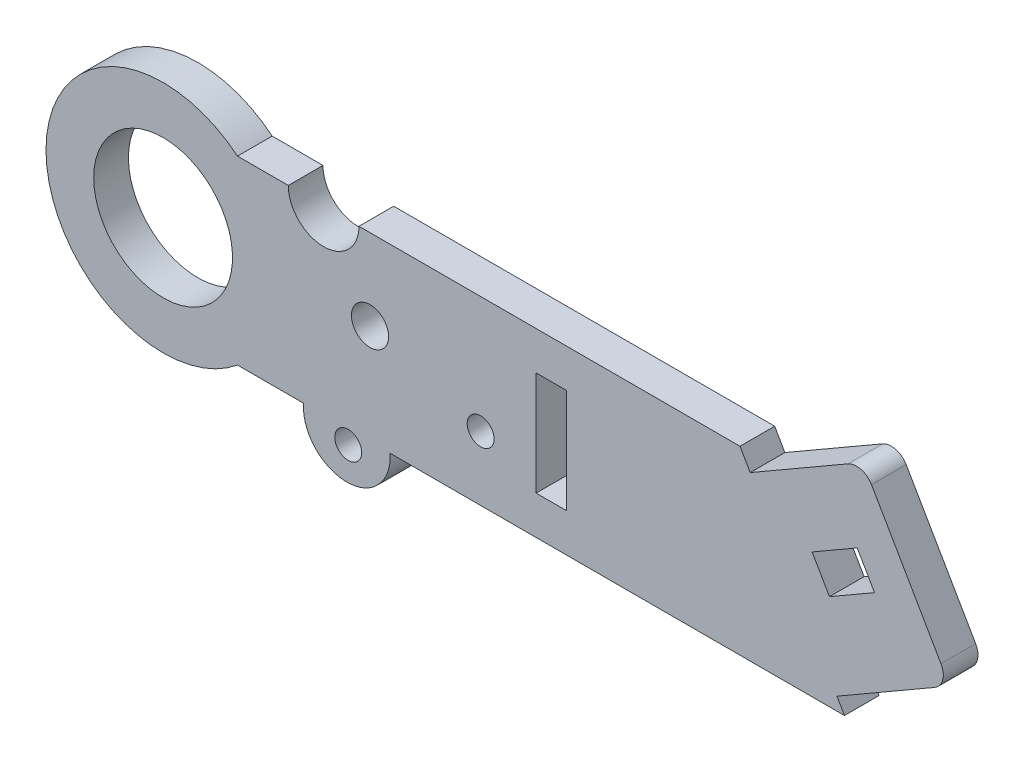
SolidWorks part; units mm, degrees
ref_plane "Ebene vorne" through (0, 0, 0) normal (0, 0, 1) x (1, 0, 0)
ref_plane "Ebene oben" through (0, 0, 0) normal (0, 1, 0) x (1, 0, 0)
ref_plane "Ebene rechts" through (0, 0, 0) normal (1, 0, 0) x (0, 0, -1)
sketch "Skizze1" plane through (0, 0, 0) normal (0, 0, 1) x (1, 0, 0)
  line L0 (8.5706, -10.4305) -> (-71.4294, -10.4305)
  line L7 (-71.4294, 10.4305) -> (-65.5753, 10.4305)
  line L8 (-57.4235, 10.4305) -> (8.5706, 10.4305)
  line L9 (-106.0055, 0) -> (28.1497, 0) construction
  arc A3 (-65.5753, 10.4305) -> (-57.4235, 10.4305) centre (-61.4994, 10.4305) ccw
  arc A6 (-71.4294, 10.4305) -> (-71.4294, -10.4305) centre (-80, 0) ccw
  arc A7 (8.5706, 10.4305) -> (8.5706, -10.4305) centre (8.5706, 0) cw
  dimension "D4" = 5.8542
  dimension "D2" = 20.861
  dimension "D1" = 13.5
  dimension "D3" = 4.0759
  dimension "D5" = 80
  dimension "D6" = 10.4305
extrude "Aufsatz-Linear austragen1" add sketch "Skizze1" along normal blind 4
sketch "Skizze2" plane through (0, 0, 4) normal (0, 0, 1) x (1, 0, 0)
  line L0 (-5.1962, 4.0336) -> (0, 7.0336)
  line L5 (-5.1962, 4.0336) -> (-3.1962, 0.5695)
  line L6 (0, 7.0336) -> (2, 3.5695)
  line L7 (-3.1962, 0.5695) -> (2, 3.5695)
  line L8 (-71.4294, -10.4305) -> (8.5706, -10.4305) construction
  line L9 (8.5706, 10.4305) -> (-57.4235, 10.4305) construction
  circle A1 centre (-80, 0) radius 8
  circle A2 centre (-56.1528, 1.1059) radius 2.1413
  dimension "D1" = 4
  dimension "D2" = 16
  dimension "D8" = 4.2826
  dimension "D3" = 6
  dimension "D4" = 14
  dimension "D5" = 80
  dimension "D6" = 56.1528
  dimension "D7" = 1.1059
  dimension "D9" = 2
  dimension "D10" = 60
extrude "Schnitt-Linear austragen1" cut sketch "Skizze2" against normal up to next
sketch "Skizze3" plane through (0, 0, 4) normal (0, 0, 1) x (1, 0, 0)
  line L0 (12.9867, 30.6283) -> (33.0198, -4.07)
  line L1 (-2.3301, -8.9305) -> (8.9282, -2.4305)
  line L2 (-15.6304, 14.1062) -> (-12.3301, 8.39)
  line L7 (-2.3301, -8.9305) -> (4.4027, -20.5921)
  line L8 (-15.6304, 14.1062) -> (12.9867, 30.6283)
  line L10 (33.0198, -4.07) -> (4.4027, -20.5921)
  line L11 (-5.1962, 4.0336) -> (-3.1962, 0.5695) construction
  line L12 (8.9282, -2.4305) -> (-1.0718, 14.89)
  line L13 (-1.0718, 14.89) -> (-12.3301, 8.39)
  line L14 (-71.4294, -10.4305) -> (8.5706, -10.4305) construction
  dimension "D1" = 20
  dimension "D2" = 1.5
  dimension "D3" = 4
  dimension "D4" = 13
extrude "Schnitt-Linear austragen2" cut sketch "Skizze3" against normal up to next
sketch "Skizze4" plane through (0, 0, 0) normal (0, 0, 1) x (1, 0, 0)
  line L0 (-8.7958, 10.4305) -> (-1.0718, 14.89)
  line L1 (1.6498, 14.1761) -> (9.6603, 0.3015)
  line L3 (-8.7958, 10.4305) -> (1.5029, 10.4305)
  line L4 (1.5029, 10.4305) -> (8.9282, -2.4305)
  line L5 (-2.3301, -8.9305) -> (-1.4641, -10.4305) construction
  arc A0 (8.9282, -2.4305) -> (9.6603, 0.3015) centre (7.9282, -0.6985) ccw
  arc A1 (-1.0718, 14.89) -> (1.6498, 14.1761) centre (-0.0717, 13.158) cw
  dimension "D2" = 2
  dimension "D3" = 2
  dimension "D1" = 15
extrude "Aufsatz-Linear austragen3" add sketch "Skizze4" along normal up to surface (4 mm away) up to face at (-54.0115, 1.1059, 4)
sketch "Skizze5" plane through (0, 0, 4) normal (0, 0, 1) x (1, 0, 0)
  line L0 (19.551, 0) -> (-121.594, 0) construction
  line L1 (-37.0082, 6) -> (-33.5082, 6)
  line L2 (-37.0082, 6) -> (-37.0082, -6)
  line L3 (-37.0082, -6) -> (-33.5082, -6)
  line L4 (-33.5082, 6) -> (-33.5082, -6)
  line L5 (-13.5082, 10.4305) -> (-57.4235, 10.4305) construction
  line L6 (-71.4294, -10.4305) -> (-1.4641, -10.4305) construction
  dimension "D1" = 3.5
  dimension "D2" = 12
  dimension "D3" = 20
extrude "Schnitt-Linear austragen3" cut sketch "Skizze5" against normal up to next contours L4 L3 L2 L1
sketch "Skizze6" plane through (0, 0, 4) normal (0, 0, 1) x (1, 0, 0)
  line L0 (-71.4294, -10.4305) -> (-1.4641, -10.4305) construction
  line L1 (-63.8117, -10.4305) -> (-53.8403, -10.4305)
  arc A0 (-63.8117, -10.4305) -> (-53.8403, -10.4305) centre (-58.826, -10.8085) ccw
  dimension "D1" = 5
  dimension "D2" = 12.6035
  dimension "D3" = 0.378
extrude "Aufsatz-Linear austragen4" add sketch "Skizze6" against normal up to surface (4 mm away) up to face at (-24.8068, 3.6325, 0)
sketch "Skizze7" plane through (0, 0, 4) normal (0, 0, 1) x (1, 0, 0)
  circle A0 centre (-58.6598, -12.0125) radius 1.55
  circle A1 centre (-43.4, -3.0251) radius 1.55
  arc A2 (-63.8117, -10.4305) -> (-53.8403, -10.4305) centre (-58.826, -10.8085) ccw construction
  dimension "D1" = 3.1
  dimension "D3" = 0.1661
  dimension "D4" = 15.2598
  dimension "D2" = 1.204
  dimension "D5" = 8.9875
extrude "Schnitt-Linear austragen4" cut sketch "Skizze7" against normal blind 10
